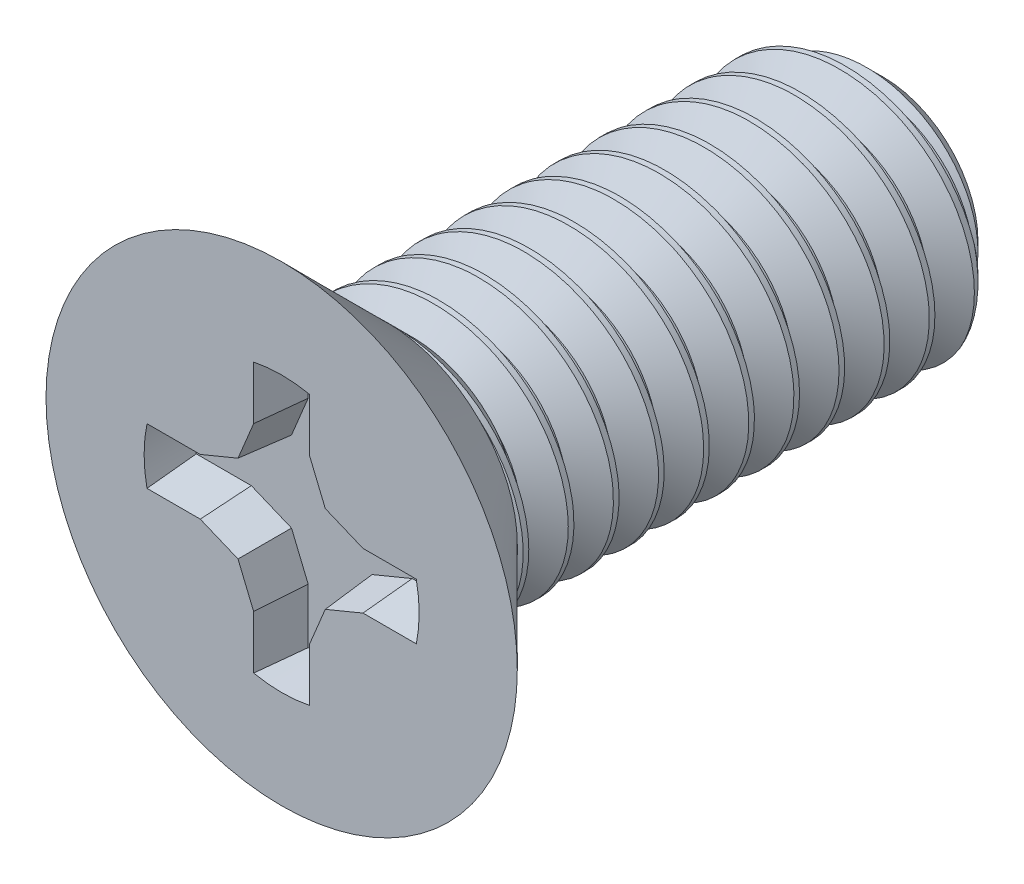
SolidWorks part; units mm, degrees
ref_plane "Front Plane" through (0, 0, 0) normal (0, 0, 1) x (1, 0, 0)
ref_plane "Top Plane" through (0, 0, 0) normal (0, 1, 0) x (1, 0, 0)
ref_plane "Right Plane" through (0, 0, 0) normal (1, 0, 0) x (0, 0, -1)
sketch "Sketch1" plane through (0, 0, 0) normal (1, 0, 0) x (0, 0, -1)
  line L0 (0, 0) -> (-1.5, 0) construction
  line L1 (-1.5, 2.35) -> (-1.5, -2.35) construction
  line L2 (-1.5, 2.35) -> (0, 0.85) construction
  line L3 (-1.5, -2.35) -> (0, -0.85) construction
  line L4 (0, 1.3) -> (0, -1.3) construction
  line L5 (0, 0) -> (4.5, 0) construction
  line L6 (0, 1.3) -> (0.45, 1.3) construction
  line L7 (0, 1.3) -> (-0.45, 1.3) construction
  line L8 (4.5, 0.85) -> (4.5, -0.85) construction
  point P6 (-1.5, 0)
  point P11 (0, 0)
  point P16 (-0.45, 1.3)
  point P17 (2.925, -1.3)
  point P20 (4.5, 0)
  point P21 (-0.75, 0)
  point P22 (2.925, -0.85)
  point P23 (4.5, -0.85)
  point P25 (4.5, 0.85)
  dimension "Head Height" = 1.5
  dimension "Head Diameter" = 4.7
  dimension "Countersink Angle" = 90
  dimension "Thread OD" = 2.6
  dimension "Length" = 6
  dimension "Thread Pitch" = 0.45
  dimension "D1" = 1.575
sketch "Sketch2" plane through (0, 0, 0) normal (0, 0, 1) x (1, 0, 0)
  line L0 (0.2794, 1.3716) -> (-0.2794, 1.3716) construction
  circle A0 centre (0, 0) radius 1.3716 construction
  point P3 (0, 1.3716)
  point P7 (0, 1.3716)
  dimension "Drive Dia" = 2.7432
  dimension "Drive Width" = 0.5588
sketch "Sketch3" plane through (0, 0, 0) normal (1, 0, 0) x (0, 0, -1)
  line L0 (-1.5, 0) -> (-1.5, 2.35)
  line L1 (-1.5, 2.35) -> (-0.45, 1.3)
  line L2 (-1.5, 2.35) -> (0, 0.85) construction
  line L3 (0, 1.3) -> (0.45, 1.3) construction
  line L4 (-1.5, 0) -> (-0.45, 0)
  line L5 (0, 0) -> (-1.5, 0) construction
  line L6 (-0.45, 0) -> (-0.45, 1.3)
revolve "Revolve1" add sketch "Sketch3" angle 360 about L4
sketch "Sketch5" plane through (0, 0, 0) normal (1, 0, 0) x (0, 0, -1)
  line L0 (4.5, 0) -> (-0.45, 0)
  line L1 (0, 0) -> (4.5, 0) construction
  line L2 (-0.45, 0) -> (-0.45, 1.3)
  line L3 (-0.45, 1.3) -> (4.1445, 1.3)
  line L4 (4.1445, 1.3) -> (4.5, 0.9445)
  line L5 (4.5, 0.9445) -> (4.5, 0)
  line L6 (4.1445, 1.3) -> (4.5, 1.3) construction
  line L7 (4.5, 1.3) -> (4.5, 0.9445) construction
  line L8 (0, 1.3) -> (0.45, 1.3) construction
  line L9 (-0.45, -1.3) -> (-0.45, 1.3) construction
  dimension "D1" = 0.3555
revolve "Revolve2" add sketch "Sketch5" angle 360 about L0
sketch "Sketch4" plane through (0, 0, 1.5) normal (0, 0, 1) x (1, 0, 0)
  line L0 (0, 0) -> (0, 1.3716)
  line L1 (0, 0) -> (1.3716, 0)
  line L2 (0, 0) -> (0.8111, 0.8111) construction
  line L3 (0.2794, 1.3428) -> (0.2794, 0.8111)
  line L4 (0.2794, 0.8111) -> (0.2794, 0.2794) construction
  line L5 (0.8111, 0.2794) -> (0.2794, 0.2794) construction
  line L6 (1.3428, 0.2794) -> (0.8111, 0.2794)
  line L7 (0.2794, 0.8111) -> (0.4351, 0.4351)
  line L8 (0.4351, 0.4351) -> (0.8111, 0.2794)
  line L9 (0, 1.3716) -> (0, 2.35) construction
  line L10 (0, 2.35) -> (0, -2.35) construction
  circle A0 centre (0, 0) radius 1.3716 construction
  arc A1 (0, 1.3716) -> (0.2794, 1.3428) centre (0, 0) cw
  arc A2 (1.3716, 0) -> (1.3428, 0.2794) centre (0, 0) ccw
  arc A3 (0.8111, 0.2794) -> (0.2794, 0.8111) centre (0.8111, 0.8111) cw construction
  circle A4 centre (0, 0) radius 2.35 construction
  point P8 (0.4351, 0.4351)
  point P22 (0, -1.3716)
  point P23 (0, 1.3716)
  dimension "D1" = 0.9784
extrude "Cut-Extrude1" cut sketch "Sketch4" against normal blind 0.5 contours L1 A2 L6 L8 L7 L3 A1 L0
pattern_circular "CirPattern1" count 4 over 360 about axis through (0, 0, 0) along (0, 0, 1) of "Cut-Extrude1"
draft "Draft2" type of draft neutral plane draft angle 5 faces to draft 16 face at (-1.077, 0.2794, 1.25) face at (-0.6231, 0.3573, 1.25) face at (-0.3573, 0.6231, 1.25) face at (-0.2794, 1.077, 1.25) face at (0.2794, 1.077, 1.25) face at (0.3573, 0.6231, 1.25) face at (0.6231, 0.3573, 1.25) face at (1.077, 0.2794, 1.25) face at (1.077, -0.2794, 1.25) face at (0.6231, -0.3573, 1.25) face at (0.3573, -0.6231, 1.25) face at (0.2794, -1.077, 1.25) face at (-0.2794, -1.077, 1.25) face at (-0.3573, -0.6231, 1.25) face at (-0.6231, -0.3573, 1.25) face at (-1.077, -0.2794, 1.25) neutral plane through (0, 0, 1.5) neutral plane normal (0, 0, 1) parameters "D1"=5
ref_plane "Plane1" through (0, 0, 0.45) normal (0, 0, -1) x (-1, 0, 0)
split "Split1" trim tools "Plane1" bodies to split 107 105 resulting bodies 108 109
sketch "Sketch6" plane through (0, 0, -4.5) normal (0, 0, 1) x (1, 0, 0)
  circle A1 centre (0, 0) radius 1.3
  circle A2 centre (0, 0) radius 1.3
  dimension "D1" = 0
curve "Helix/Spiral1" pitch 0.45 height 6 turns 13.3333
sketch "Sketch7" plane through (0, 0, 0) normal (1, 0, 0) x (0, 0, -1)
  line L0 (4.4719, 1.3487) -> (4.9219, 1.3487) construction
  line L1 (4.4719, 1.3487) -> (4.6969, 0.959) construction
  line L2 (4.6969, 0.959) -> (4.9219, 1.3487) construction
  line L3 (4.6688, 1.0077) -> (4.725, 1.0077) construction
  line L4 (4.5, 1.3) -> (4.8938, 1.3) construction
  line L5 (4.6969, 1.3) -> (4.6969, 1.3487) construction
  line L6 (4.6969, 1.0077) -> (4.6969, 0.959) construction
  line L7 (4.6969, 1.3244) -> (4.4859, 1.3244) construction
  line L10 (4.725, 1.0077) -> (4.6688, 1.0077)
  line L11 (4.4859, 1.3244) -> (4.6688, 1.0077)
  line L12 (4.4859, 1.3244) -> (4.9078, 1.3244)
  line L13 (4.9078, 1.3244) -> (4.725, 1.0077)
  dimension "D1" = 0.45
  dimension "D2" = 0.0563
sweep "Cut-Sweep1" cut profiles "Sketch7" path "Helix/Spiral1"
combine bodies "Combine1" operation type add bodies to combine 109 110
ref_plane "Plane2" through (0, 0, 0.45) normal (0, 0, 1) x (1, 0, 0)
sketch "Sketch8" plane through (0, 0, 0.45) normal (0, 0, 1) x (1, 0, 0)
  circle A0 centre (0, 0) radius 1.3
extrude "Boss-Extrude1" add sketch "Sketch8" against normal up to vertex draft 45
equation "\"D1@Sketch5\" = \"Thread Pitch@Sketch1\" * .79"
equation "\"D4@Helix/Spiral1\" = \"Thread Pitch@Sketch1\""
equation "\"D3@Helix/Spiral1\"=\"Length@Sketch1\""
equation "\"D1@Sketch7\" = \"Thread Pitch@Sketch1\""
equation "\"D2@Sketch7\" = \"Thread Pitch@Sketch1\" / 8"
equation "\"D1@Sketch1\"=\"Thread Pitch@Sketch1\"*3.5"
equation "\"D1@Cut-Extrude1\"=\"Head Height@Sketch1\"/3"
